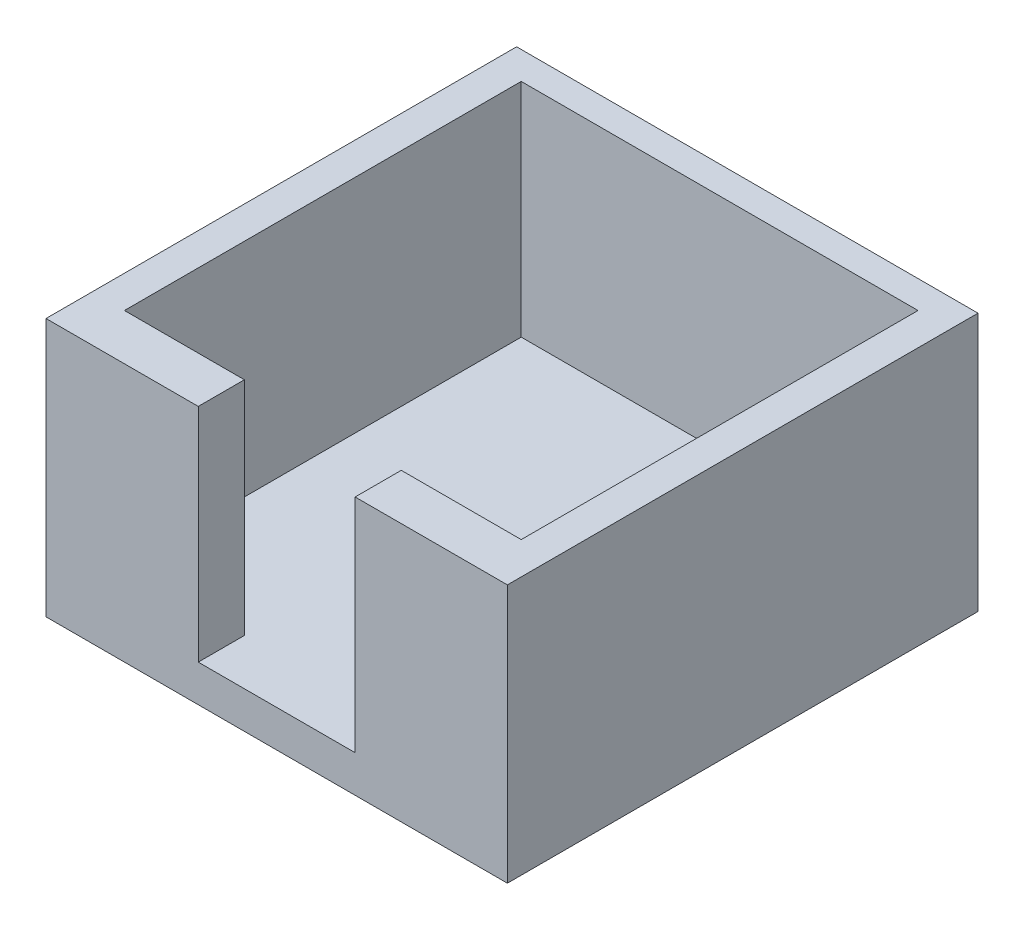
SolidWorks part; units mm, degrees
ref_plane "Front Plane" through (0, 0, 0) normal (0, 0, 1) x (1, 0, 0)
ref_plane "Top Plane" through (0, 0, 0) normal (0, 1, 0) x (1, 0, 0)
ref_plane "Right Plane" through (0, 0, 0) normal (1, 0, 0) x (0, 0, -1)
sketch "Sketch1" plane through (0, 0, 0) normal (0, 1, 0) x (1, 0, 0)
  line L1 (0, 0) -> (50, 0)
  line L2 (0, 0) -> (0, 51)
  line L3 (0, 51) -> (50, 51)
  line L4 (50, 0) -> (50, 51)
  dimension "D1" = 50
  dimension "D2" = 51
extrude "Boss-Extrude1" add sketch "Sketch1" along normal blind 28
sketch "Sketch2" plane through (0, 28, 0) normal (0, 1, 0) x (1, 0, 0)
  line L0 (0, 0) -> (50, 0) construction
  line L2 (16.5, 5) -> (16.5, 0)
  line L3 (16.5, 0) -> (33.5, 0)
  line L4 (33.5, 5) -> (33.5, 0)
  line L5 (16.5, 5) -> (3.5, 5)
  line L6 (46.5, 5) -> (33.5, 5)
  line L7 (46.5, 5) -> (46.5, 48)
  line L8 (46.5, 48) -> (3.5, 48)
  line L9 (3.5, 5) -> (3.5, 48)
  point P6 (25, 48)
  point P7 (25, 0)
  point P12 (25, 0)
  dimension "D1" = 5
  dimension "D2" = 17
  dimension "D3" = 43
  dimension "D4" = 43
extrude "Cut-Extrude1" cut sketch "Sketch2" against normal blind 24
